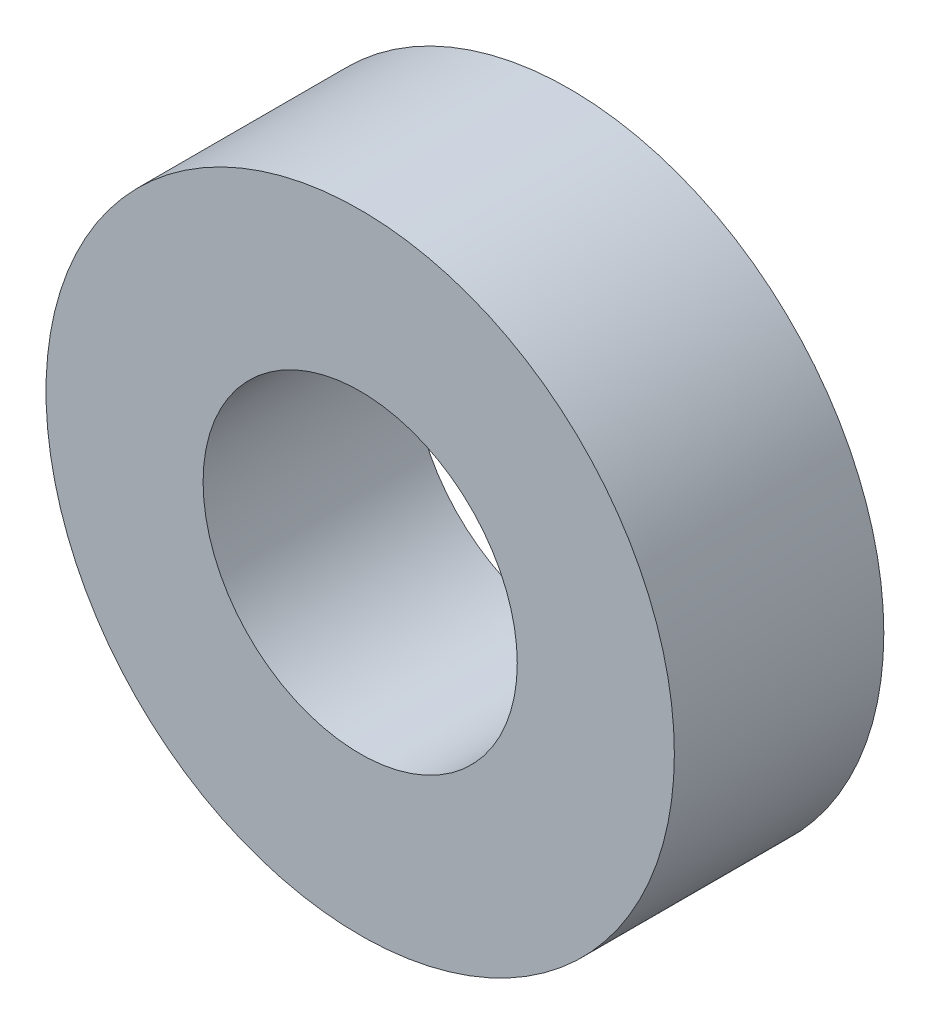
SolidWorks part; units mm, degrees
ref_plane "Front Plane" through (0, 0, 0) normal (0, 0, 1) x (1, 0, 0)
ref_plane "Top Plane" through (0, 0, 0) normal (0, 1, 0) x (1, 0, 0)
ref_plane "Right Plane" through (0, 0, 0) normal (1, 0, 0) x (0, 0, -1)
sketch "Sketch1" plane through (0, 0, 0) normal (0, 0, 1) x (1, 0, 0)
  circle A0 centre (0, 0) radius 1.5
  circle A1 centre (0, 0) radius 3
  dimension "D1" = 3
  dimension "D2" = 6
extrude "Boss-Extrude1" add sketch "Sketch1" along normal blind 2
